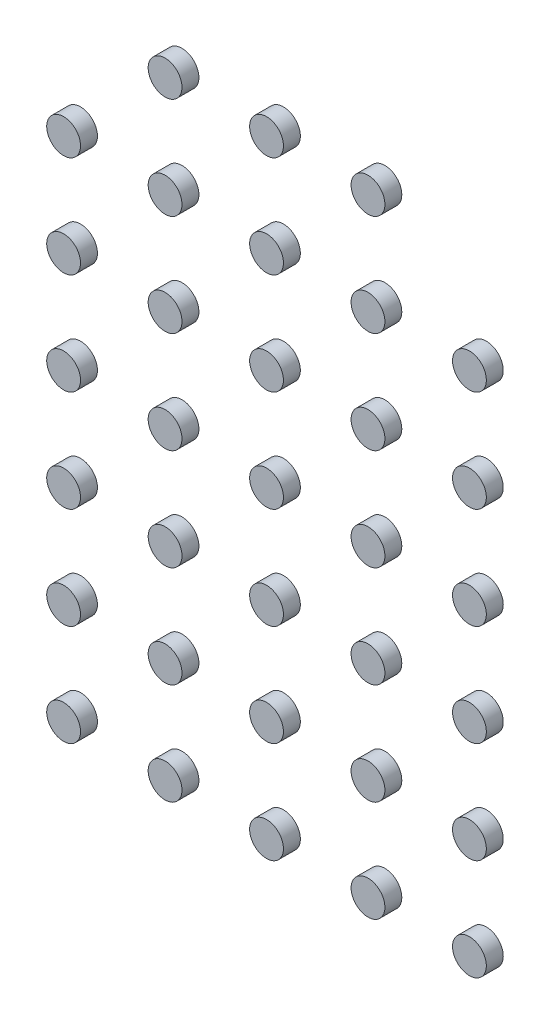
SolidWorks part; units mm, degrees
ref_plane "前视基准面" through (0, 0, 0) normal (0, 0, 1) x (1, 0, 0)
ref_plane "上视基准面" through (0, 0, 0) normal (0, 1, 0) x (1, 0, 0)
ref_plane "右视基准面" through (0, 0, 0) normal (1, 0, 0) x (0, 0, -1)
other "Configuration Table"
sketch "草图1" plane through (0, 0, 0) normal (0, 0, 1) x (1, 0, 0)
  line L0 (-0.7, 0) -> (0.7, 0)
  arc A0 (0.7, 0) -> (-0.7, 0) centre (0, 0) ccw
  dimension "D1" = 1.4
sketch "草图4" plane through (0, 0, 0) normal (0, 0, 1) x (1, 0, 0)
  circle A0 centre (0, 0) radius 0.5
  dimension "D1" = 1
extrude "凸台-拉伸2" add sketch "草图4" along normal blind 0.5
ref_plane "基准面1" through (0, 9, 0) normal (0, 1, 0) x (1, 0, 0)
ref_plane "基准面2" through (6, 0, 0) normal (1, 0, 0) x (0, 0, -1)
delete or keep bodies "实体-删除/保留 1" [suppressed] type delete bodies bodies 265 270 275 280 285 264 269 279 284 263 283 274
sketch "草图5" plane through (0, 0, 0.5) normal (0, 0, 1) x (1, 0, 0)
  circle A1 centre (0, 0) radius 0.5
  circle A2 centre (0, 0) radius 0.5
  dimension "D1" = 0
sketch "草图6" plane through (0, 0, 0) normal (0, 0, 1) x (1, 0, 0)
  circle A1 centre (0, 0) radius 0.5
  circle A2 centre (0, 0) radius 0.5
  dimension "D1" = 0
pattern_linear "阵列(线性)1" count 5 spacing 3 along (1, 0, 0) count 6 spacing 3 along (0, 1, 0) of "凸台-拉伸2"
delete or keep bodies "实体-删除/保留 2" type delete bodies bodies 314 318
pattern_linear "阵列(线性)2" count 5 spacing 3 along (1, 0, 0) count 2 spacing 3 along (0, -1, 0) of "凸台-拉伸2"
